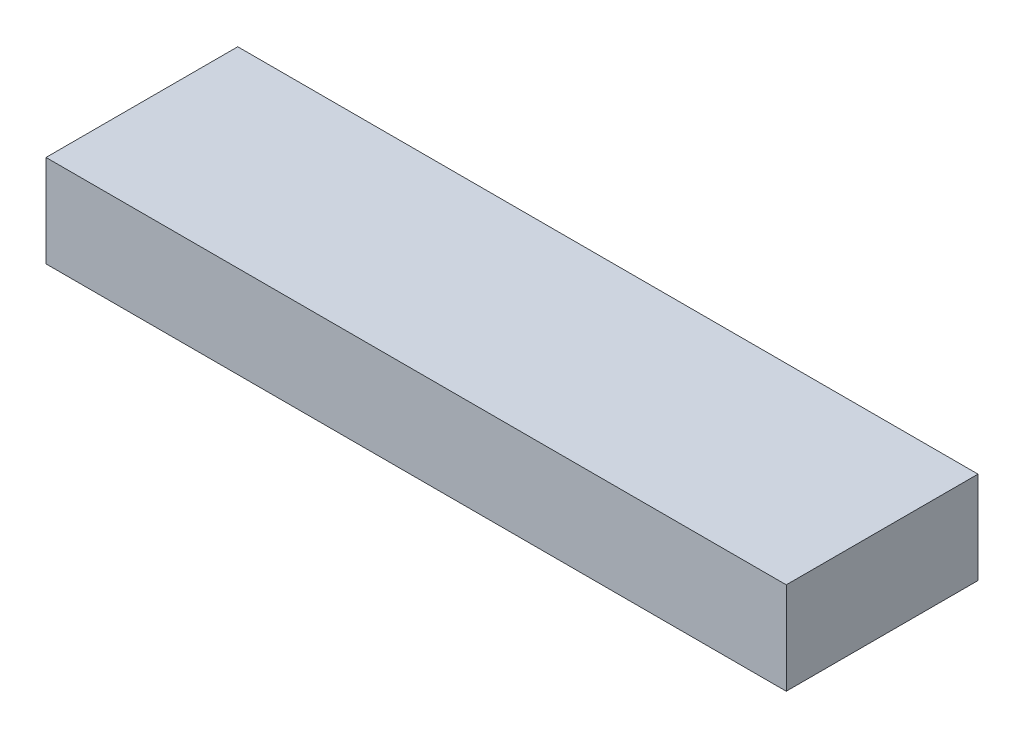
SolidWorks part; units mm, degrees
ref_plane "Front Plane" through (0, 0, 0) normal (0, 0, 1) x (1, 0, 0)
ref_plane "Top Plane" through (0, 0, 0) normal (0, 1, 0) x (1, 0, 0)
ref_plane "Right Plane" through (0, 0, 0) normal (1, 0, 0) x (0, 0, -1)
sketch "Sketch1" plane through (0, 0, 0) normal (0, 1, 0) x (1, 0, 0)
  line L1 (-89.1748, 31.2886) -> (-8.8748, 31.2886)
  line L2 (-89.1748, 31.2886) -> (-89.1748, 10.4886)
  line L3 (-89.1748, 10.4886) -> (-8.8748, 10.4886)
  line L4 (-8.8748, 31.2886) -> (-8.8748, 10.4886)
  line L5 (-89.1748, 31.2886) -> (-8.8748, 10.4886) construction
  line L6 (-89.1748, 10.4886) -> (-8.8748, 31.2886) construction
  point P0 (-49.0248, 20.8886)
  dimension "D1" = 20.8
  dimension "D2" = 80.3
extrude "Boss-Extrude1" add sketch "Sketch1" along normal blind 10
